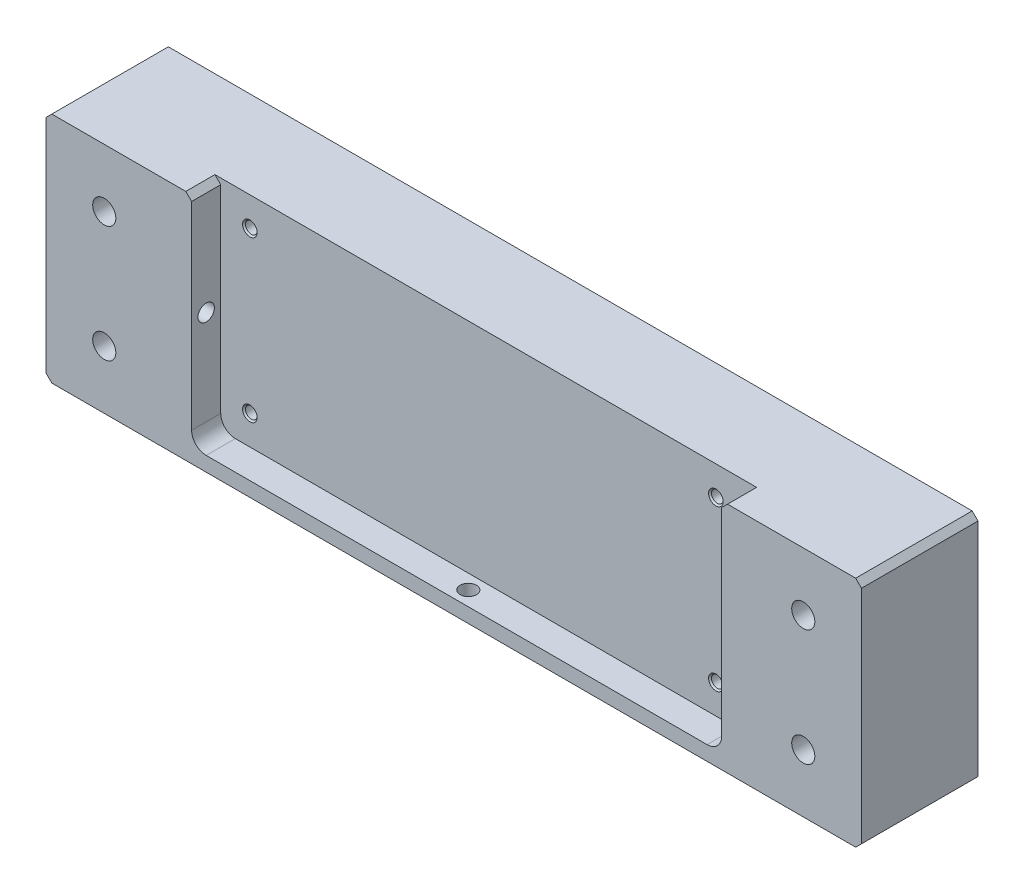
SolidWorks part; units mm, degrees
material "6061 Alloy"
ref_plane "Front" through (0, 0, 0) normal (0, 0, 1) x (1, 0, 0)
ref_plane "Top" through (0, 0, 0) normal (0, 1, 0) x (1, 0, 0)
ref_plane "Right" through (0, 0, 0) normal (1, 0, 0) x (0, 0, -1)
sketch "Sketch1" plane through (0, 0, 0) normal (0, 0, 1) x (1, 0, 0)
  line L1 (-177.8, 50.8) -> (177.8, 50.8)
  line L2 (-177.8, 50.8) -> (-177.8, -50.8)
  line L3 (-177.8, -50.8) -> (177.8, -50.8)
  line L4 (177.8, 50.8) -> (177.8, -50.8)
  line L5 (-177.8, 50.8) -> (177.8, -50.8) construction
  line L6 (-177.8, -50.8) -> (177.8, 50.8) construction
  point P0 (0, 0)
  dimension "D1" = 355.6
  dimension "D2" = 101.6
extrude "Extrude1" add sketch "Sketch1" along normal blind 50.8
sketch "Sketch6" plane through (0, 0, 50.8) normal (0, 0, 1) x (1, 0, 0)
  line L1 (177.8, 50.8) -> (-177.8, 50.8) construction
  line L2 (116.84, 50.8) -> (-114.3, 50.8)
  line L3 (116.84, 50.8) -> (116.84, -44.45)
  line L4 (116.84, -44.45) -> (-114.3, -44.45)
  line L5 (-114.3, 50.8) -> (-114.3, -44.45)
  dimension "D1" = 114.3
  dimension "D2" = 95.25
  dimension "D3" = 231.14
extrude "Extrude2" cut sketch "Sketch6" against normal blind 12.7
fillet "Fillet1" radius 6.35 2 edges at (-114.3, -44.45, 44.45) (116.84, -44.45, 44.45)
hole_wizard "1/4-20 Tapped Hole1" positions "Sketch8" profile "Sketch7" tap size "1/4-20" standard "Ansi Inch"
sketch "Sketch8" plane through (0, 0, 38.1) normal (0, 0, 1) x (1, 0, 0)
  point P0 (101.6, -31.75)
  dimension "D1" = 101.6
  dimension "D2" = 31.75
cosmetic thread "Hole Thread1" parameters "D1"=10.16, "D2"=6.35
sketch "Sketch7" plane through (101.6, -31.75, 38.1) normal (1, 0, 0) x (0, -1, 0)
  line L0 (0, 0) -> (0, 15.5038)
  line L1 (0, 15.5038) -> (2.5527, 13.97)
  line L2 (2.5527, 13.97) -> (2.5527, 0.635)
  line L3 (2.5527, 0.635) -> (3.1877, 0)
  line L5 (3.1877, 0) -> (0, 0)
  line L6 (-2.5527, 0.635) -> (-3.1877, 0) construction
  line L10 (0, 15.5038) -> (-2.5527, 13.97) construction
  line L11 (0, -6.35) -> (0, 107.95) construction
  dimension "Tap Drill Dia." = 5.1054
  dimension "Tap Drill Depth" = 13.97
  dimension "Near C'Sink Dia." = 6.3754
  dimension "Near C'Sink Angle" = 90
  dimension "Drill Angle" = 118
pattern_linear "LPattern3" count 2 spacing 203.2 along (-1, 0, 0) count 2 spacing 69.85 along (0, 1, 0) of "1/4-20 Tapped Hole1"
hole_wizard "1/4 Clearance Hole2" positions "Sketch11" profile "Sketch10" hole size "1/4" standard "Ansi Inch" end condition up to next
sketch "Sketch11" plane through (-177.8, 0, 0) normal (-1, 0, 0) x (0, 0, 1)
  point P0 (44.45, 3.175)
  dimension "D1" = 44.45
  dimension "D2" = 3.175
sketch "Sketch10" plane through (-177.8, 3.175, 44.45) normal (0, 1, 0) x (0, 0, 1)
  line L0 (0, 0) -> (0, 63.5)
  line L1 (0, 63.5) -> (3.5712, 63.5)
  line L2 (3.5712, 63.5) -> (3.5712, 0)
  line L5 (3.5712, 0) -> (0, 0)
  line L11 (0, -6.35) -> (0, 107.95) construction
  dimension "Thru Hole Dia." = 7.1425
  dimension "Thru Hole Depth" = 63.5
hole_wizard "1/4 Clearance Hole1" positions "Sketch13" profile "Sketch12" hole size "1/4" standard "Ansi Inch" end condition through all
sketch "Sketch13" plane through (0, -50.8, 0) normal (0, -1, 0) x (1, 0, 0)
  point P0 (0, 44.45)
  dimension "D1" = 44.45
sketch "Sketch12" plane through (0, -50.8, 44.45) normal (1, 0, 0) x (0, 0, -1)
  line L0 (0, 0) -> (0, 101.6)
  line L1 (0, 101.6) -> (3.5712, 101.6)
  line L2 (3.5712, 101.6) -> (3.5712, 0)
  line L5 (3.5712, 0) -> (0, 0)
  line L11 (0, -6.35) -> (0, 107.95) construction
  dimension "Thru Hole Dia." = 7.1425
  dimension "Thru Hole Depth" = 101.6
hole_wizard "CBORE for 3/8 Socket Head Cap Screw1" positions "Sketch15" profile "Sketch14" counterbore size "3/8" standard "Ansi Inch" end condition through all
sketch "Sketch15" plane through (0, 0, 0) normal (0, 0, -1) x (-1, 0, 0)
  point P0 (-152.4, 25.4)
  dimension "D1" = 152.4
  dimension "D2" = 25.4
sketch "Sketch14" plane through (152.4, 25.4, 0) normal (1, 0, 0) x (0, 1, 0)
  line L0 (0, 0) -> (0, 50.8)
  line L1 (0, 50.8) -> (5.0419, 50.8)
  line L3 (5.0419, 50.8) -> (5.0419, 9.525)
  line L4 (7.9375, 9.525) -> (5.0419, 9.525)
  line L5 (7.9375, 9.525) -> (7.9375, 0.635)
  line L6 (7.9375, 0.635) -> (8.5725, 0)
  line L7 (8.5725, 0) -> (0, 0)
  line L8 (-7.9375, 0.635) -> (-8.5725, 0) construction
  line L11 (0, -6.35) -> (0, 107.95) construction
  dimension "Thru Hole Dia." = 10.0838
  dimension "Thru Hole Depth" = 50.8
  dimension "C'Bore Dia." = 15.875
  dimension "C'Bore Depth" = 9.525
  dimension "Near C'Sink Dia." = 17.145
  dimension "Near C'Sink Angle" = 90
pattern_linear "LPattern4" count 2 spacing 50.8 along (0, -1, 0) count 2 spacing 304.8 along (-1, 0, 0) of "CBORE for 3/8 Socket Head Cap Screw1"
chamfer "Chamfer1" distance 2.54 angle 45 6 edges at (-177.8, 50.8, 25.4) (-114.3, 50.8, 44.45) (116.84, 50.8, 44.45) (177.8, 50.8, 25.4) (177.8, -50.8, 25.4) (-177.8, -50.8, 25.4)
